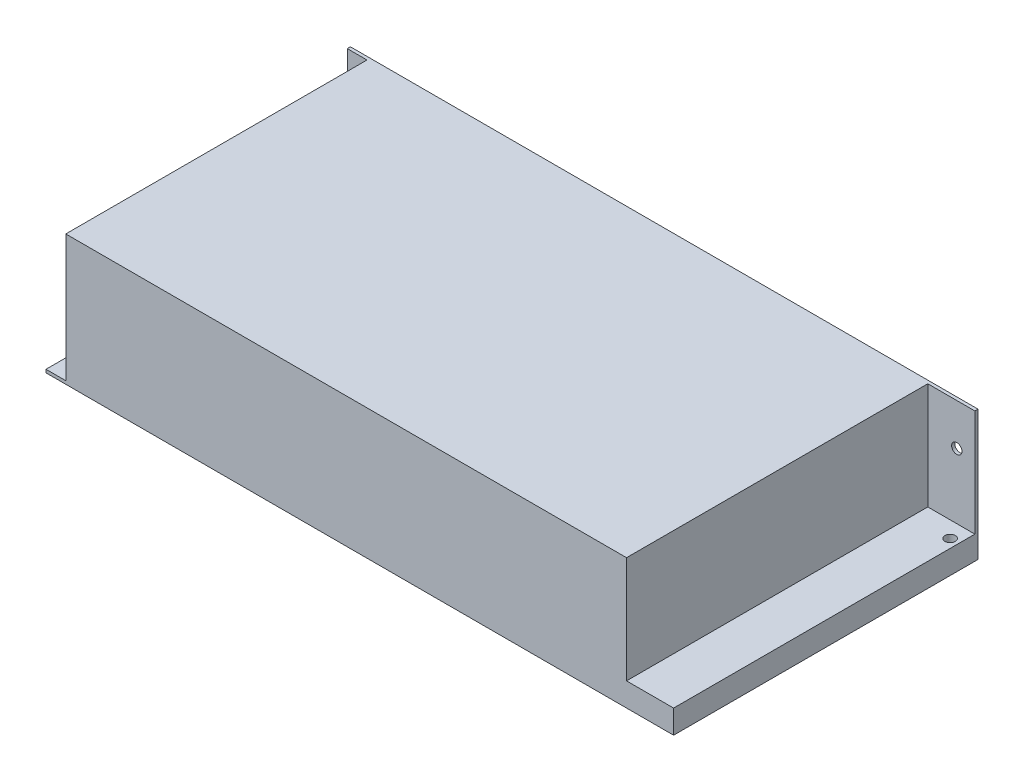
SolidWorks part; units mm, degrees
material "1060 Alloy"
ref_plane "Front Plane" through (0, 0, 0) normal (0, 0, 1) x (1, 0, 0)
ref_plane "Top Plane" through (0, 0, 0) normal (0, 1, 0) x (1, 0, 0)
ref_plane "Right Plane" through (0, 0, 0) normal (1, 0, 0) x (0, 0, -1)
sketch "Sketch1" plane through (0, 0, 0) normal (0, 1, 0) x (1, 0, 0)
  line L1 (-100, -48.5) -> (100, -48.5)
  line L2 (-100, -48.5) -> (-100, 48.5)
  line L3 (-100, 48.5) -> (100, 48.5)
  line L4 (100, -48.5) -> (100, 48.5)
  line L5 (-100, -48.5) -> (100, 48.5) construction
  line L6 (-100, 48.5) -> (100, -48.5) construction
  point P0 (0, 0)
  dimension "D1" = 97
  dimension "D2" = 200
extrude "Boss-Extrude1" add sketch "Sketch1" along normal mid plane 41.5
sketch "Sketch2" plane through (0, 20.75, 0) normal (0, 1, 0) x (1, 0, 0)
  line L0 (100, 48.5) -> (-100, 48.5) construction
  line L1 (100, -48.5) -> (85, -48.5)
  line L2 (100, -48.5) -> (100, 47.5)
  line L3 (100, 47.5) -> (85, 47.5)
  line L4 (85, -48.5) -> (85, 47.5)
  dimension "D1" = 15
  dimension "D2" = 1
extrude "Cut-Extrude1" cut sketch "Sketch2" against normal offset from surface (34 mm away) 7.5 up to face at (0, -20.75, 0)
sketch "Sketch3" plane through (0, 20.75, 0) normal (0, 1, 0) x (1, 0, 0)
  line L1 (-100, 47.5) -> (-93.7, 47.5)
  line L2 (-100, 47.5) -> (-100, -48.5)
  line L3 (-100, -48.5) -> (-93.7, -48.5)
  line L4 (-93.7, 47.5) -> (-93.7, -48.5)
  line L5 (100, 48.5) -> (-100, 48.5) construction
  dimension "D1" = 6.3
  dimension "D2" = 1
extrude "Cut-Extrude2" cut sketch "Sketch3" against normal offset from surface (40.5 mm away) 1 up to face at (0, -20.75, 0)
sketch "Sketch4" plane through (0, 0, -47.5) normal (0, 0, 1) x (1, 0, 0)
  line L0 (100, 20.75) -> (85, 20.75) construction
  line L2 (100, -13.25) -> (100, 20.75) construction
  line L3 (-96.35, 9.25) -> (-100, 9.25)
  line L4 (-100, -19.75) -> (-100, 20.75) construction
  line L5 (-100, 9.25) -> (-100, 5.95)
  line L6 (-100, 5.95) -> (-96.35, 5.95)
  line L7 (-93.7, 20.75) -> (-100, 20.75) construction
  circle A0 centre (94.25, 7.5) radius 1.65
  arc A1 (-96.35, 5.95) -> (-96.35, 9.25) centre (-96.35, 7.6) ccw
  dimension "D1" = 3.3
  dimension "D3" = 4.1
  dimension "D4" = 1.65
  dimension "D6" = 5.3
  dimension "D2" = 11.6
  dimension "D5" = 11.5
extrude "Cut-Extrude3" cut sketch "Sketch4" against normal through all
sketch "Sketch5" plane through (0, -20.75, 0) normal (0, -1, 0) x (1, 0, 0)
  line L1 (100, 48.5) -> (100, -48.5) construction
  line L2 (100, -48.5) -> (-100, -48.5) construction
  circle A0 centre (97.25, -42.35) radius 1.65
  dimension "D1" = 3.3
  dimension "D2" = 1.1
  dimension "D3" = 4.5
extrude "Cut-Extrude4" cut sketch "Sketch5" against normal through all
